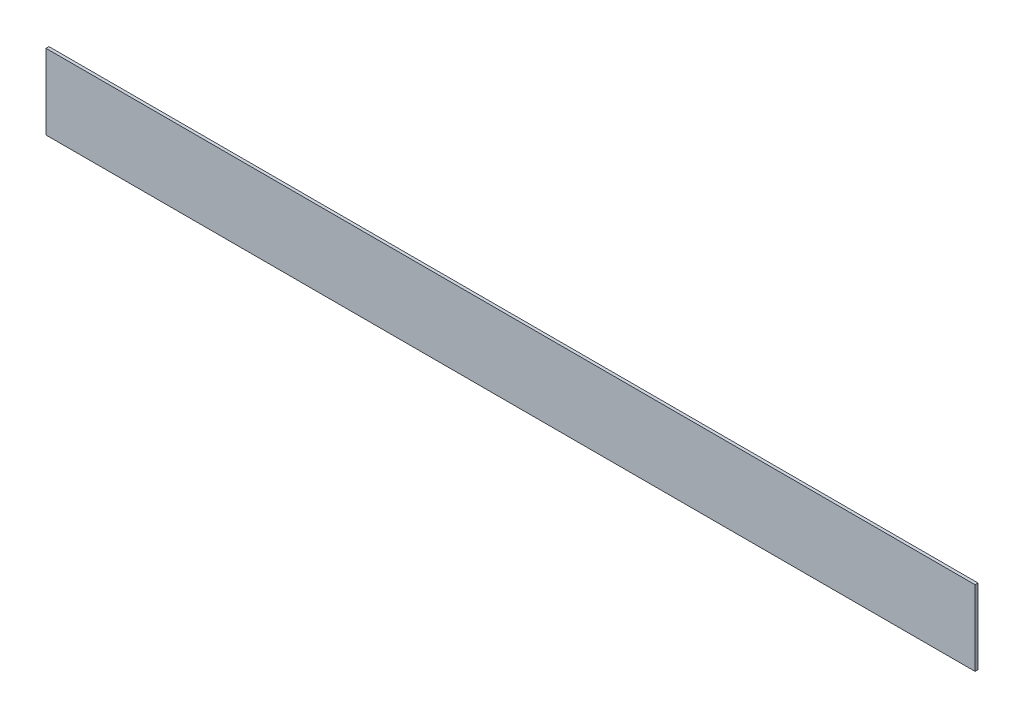
SolidWorks part; units mm, degrees
material "Glass"
ref_plane "Front Plane" through (0, 0, 0) normal (0, 0, 1) x (1, 0, 0)
ref_plane "Top Plane" through (0, 0, 0) normal (0, 1, 0) x (1, 0, 0)
ref_plane "Right Plane" through (0, 0, 0) normal (1, 0, 0) x (0, 0, -1)
sketch "Sketch1" plane through (0, 0, 0) normal (0, 0, 1) x (1, 0, 0)
  line L0 (0, 0) -> (2984.5, 0)
  line L1 (0, 0) -> (0, 241.3)
  line L2 (0, 241.3) -> (2984.5, 241.3)
  line L3 (2984.5, 241.3) -> (2984.5, 0)
  dimension "D1" = 2984.5
  dimension "D2" = 241.3
extrude "Boss-Extrude1" add sketch "Sketch1" along normal blind 9.525
